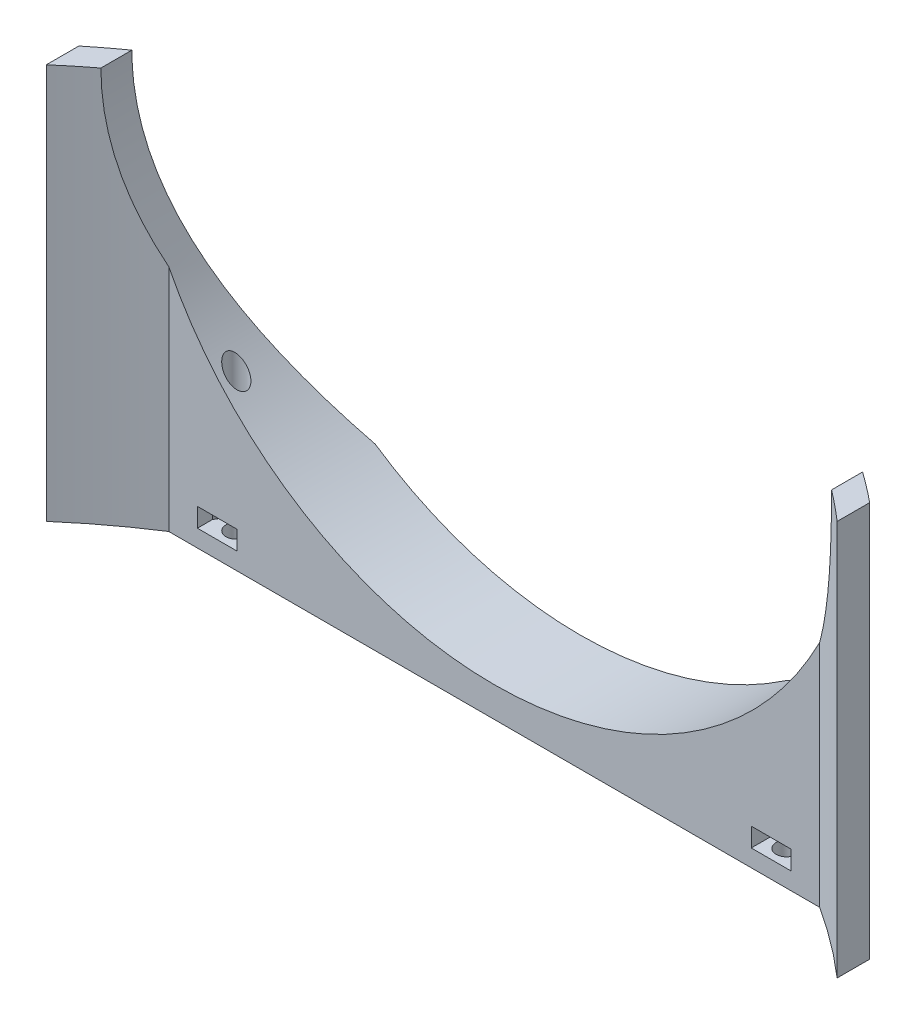
SolidWorks part; units mm, degrees
ref_plane "Front Plane" through (0, 0, 0) normal (0, 0, 1) x (1, 0, 0)
ref_plane "Top Plane" through (0, 0, 0) normal (0, 1, 0) x (1, 0, 0)
ref_plane "Right Plane" through (0, 0, 0) normal (1, 0, 0) x (0, 0, -1)
sketch "Sketch1" plane through (0, 0, 0) normal (0, 1, 0) x (1, 0, 0)
  line L1 (-46, 15.5) -> (46, 15.5)
  line L2 (-46, 15.5) -> (-46, -15.5)
  line L3 (-46, -15.5) -> (46, -15.5)
  line L4 (46, 15.5) -> (46, -15.5)
  line L5 (-46, 15.5) -> (46, -15.5) construction
  line L6 (-46, -15.5) -> (46, 15.5) construction
  point P0 (0, 0)
  dimension "D1" = 31
  dimension "D2" = 92
extrude "Boss-Extrude1" add sketch "Sketch1" along normal blind 46
sketch "Sketch2" plane through (0, 46, 0) normal (0, 1, 0) x (1, 0, 0)
  line L0 (-46, -15.5) -> (46, -15.5) construction
  circle A0 centre (0, -53.5) radius 73
  circle A1 centre (0, -53.5) radius 103
  dimension "D2" = 146
  dimension "D3" = 30
  dimension "D1" = 38
extrude "Cut-Extrude1" cut sketch "Sketch2" against normal through all
sketch "Sketch7" plane through (0, 0, 0) normal (0, -1, 0) x (1, 0, 0)
  line L0 (-46, 15.5) -> (46, 15.5) construction
  line L1 (-46, -3.1833) -> (-46, 15.5) construction
  line L2 (46, 15.5) -> (46, -3.1833) construction
  circle A0 centre (-32, -7.5) radius 1.2
  circle A1 centre (32, -7.5) radius 1.2
  dimension "D5" = 2.4
  dimension "D6" = 2.4
  dimension "D1" = 23
  dimension "D2" = 14
  dimension "D3" = 23
  dimension "D4" = 14
extrude "Cut-Extrude5" cut sketch "Sketch7" against normal through all
sketch "Sketch3" plane through (0, 46, 0) normal (0, 1, 0) x (1, 0, 0)
  line L0 (-46, -15.5) -> (46, -15.5) construction
  line L1 (-37.8551, 5.5) -> (37.8551, 5.5)
  arc A0 (-37.8551, 5.5) -> (37.8551, 5.5) centre (0, -53.5) ccw
  dimension "D1" = 70.1
  dimension "D2" = 38
  dimension "D3" = 59
extrude "Cut-Extrude2" cut sketch "Sketch3" against normal through all
sketch "Sketch5" plane through (0, 0, -15.5) normal (0, 0, -1) x (-1, 0, 0)
  line L0 (-23.8328, 46) -> (23.8328, 46) construction
  circle A0 centre (0, 46) radius 42.5
  dimension "D1" = 85
extrude "Cut-Extrude4" cut sketch "Sketch5" against normal through all
sketch "Sketch8" plane through (0, 0, 0) normal (0, -1, 0) x (1, 0, 0)
  line L4 (-34.5236, -7.2291) -> (-33.1836, -9.55)
  line L5 (-33.1836, -9.55) -> (-30.8164, -9.55)
  line L6 (-30.8164, -9.55) -> (-29.9048, -7.9709)
  line L7 (0, -5.5) -> (0, -15.5) construction
  line L10 (-34.5236, -7.2291) -> (-34.5236, -4.9723)
  line L11 (-33.9919, -6.85) -> (-34.5692, -7.85)
  line L12 (-29.6929, -7.3959) -> (-30.2703, -6.3959)
  line L13 (-30.9366, -5.45) -> (-33.246, -5.45)
  line L14 (-34.5236, -4.9723) -> (-29.9048, -4.9723)
  line L15 (-29.9048, -4.9723) -> (-29.9048, -7.9709)
  line L16 (37.8551, -5.5) -> (-37.8551, -5.5) construction
  line L17 (23.8328, -15.5) -> (-23.8328, -15.5) construction
  line L18 (29.9048, -4.9723) -> (29.9048, -7.9709)
  line L19 (34.5236, -4.9723) -> (29.9048, -4.9723)
  line L20 (34.5236, -7.2291) -> (34.5236, -4.9723)
  line L21 (30.8164, -9.55) -> (29.9048, -7.9709)
  line L22 (33.1836, -9.55) -> (30.8164, -9.55)
  line L23 (34.5236, -7.2291) -> (33.1836, -9.55)
  arc A0 (-33.5132, -8.9791) -> (-29.9625, -8.0709) centre (-32, -7.5) ccw construction
  arc A1 (33.5132, -8.9791) -> (29.9625, -8.0709) centre (32, -7.5) cw construction
  dimension "D1" = 4.6188
  dimension "D2" = 2.05
extrude "Cut-Extrude6" cut sketch "Sketch8" against normal blind 2.2 from offset 2
